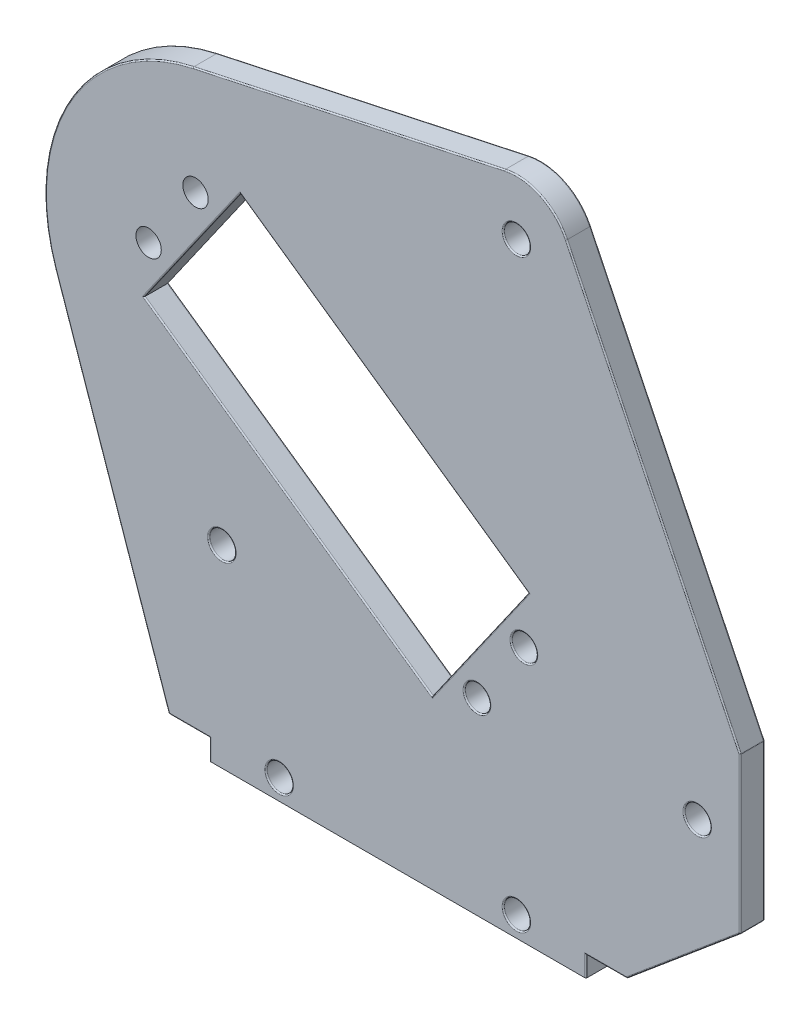
SolidWorks part; units mm, degrees
ref_plane "Front Plane" through (0, 0, 0) normal (0, 0, 1) x (1, 0, 0)
ref_plane "Top Plane" through (0, 0, 0) normal (0, 1, 0) x (1, 0, 0)
ref_plane "Right Plane" through (0, 0, 0) normal (1, 0, 0) x (0, 0, -1)
sketch "Sketch1" plane through (0, 0, 0) normal (0, 0, 1) x (1, 0, 0)
  line L0 (-25.0297, 79.9436) -> (13.0723, 88.1382) construction
  line L1 (41.85, 40.6215) -> (20.6106, 84.4605) construction
  line L2 (41.85, 21.6215) -> (41.85, 40.6215) construction
  line L3 (28, 10) -> (41.85, 21.6215) construction
  line L4 (23, 10) -> (28, 10) construction
  line L5 (23, 0) -> (23, 10) construction
  line L6 (-23, 0) -> (23, 0) construction
  line L7 (-23, 0) -> (-23, 10) construction
  line L8 (-23, 10) -> (-28, 10) construction
  line L9 (-28, 10) -> (-41.8438, 50.1182) construction
  line L10 (-25.0297, 79.9436) -> (13.0723, 88.1382)
  line L11 (41.85, 40.6215) -> (20.6106, 84.4605)
  line L12 (41.85, 21.6215) -> (41.85, 40.6215)
  line L13 (28, 10) -> (41.85, 21.6215)
  line L14 (23, 10) -> (28, 10)
  line L15 (23, 0) -> (23, 10)
  line L16 (-23, 0) -> (23, 0)
  line L17 (-23, 0) -> (-23, 10)
  line L18 (-23, 10) -> (-28, 10)
  line L19 (-28, 10) -> (-41.8438, 50.1182)
  line L20 (0, 0) -> (0, 12.9654) construction
  line L21 (-19.2558, 69.4178) -> (-31.0141, 52.6252)
  line L22 (-19.2558, 69.4178) -> (15.9678, 44.754)
  line L23 (-31.0141, 52.6252) -> (4.2095, 27.9614)
  line L24 (15.9678, 44.754) -> (4.2095, 27.9614)
  line L25 (-25.1349, 61.0215) -> (10.0886, 36.3577) construction
  line L26 (-7.5231, 48.6896) -> (-13.4023, 40.2933) construction
  line L27 (10.0886, 36.3577) -> (16.1909, 32.0848) construction
  arc A0 (20.6106, 84.4605) -> (13.0723, 88.1382) centre (14.5, 81.5) ccw construction
  arc A1 (-25.0297, 79.9436) -> (-41.8438, 50.1182) centre (-20.22, 57.58) ccw construction
  arc A2 (20.6106, 84.4605) -> (13.0723, 88.1382) centre (14.5, 81.5) ccw
  arc A3 (-25.0297, 79.9436) -> (-41.8438, 50.1182) centre (-20.22, 57.58) ccw
  circle A5 centre (9.6782, 30.5412) radius 1.55
  circle A6 centre (15.414, 38.7327) radius 1.55
  circle A7 centre (-24.7245, 66.8379) radius 1.55
  circle A8 centre (-30.4603, 58.6464) radius 1.55
  point P4 (-14.5, 10)
  point P6 (14.5, 10)
  point P8 (36.6, 31.1215)
  point P10 (-21.5, 31.1215)
  point P12 (14.5, 81.5)
  point P17 (41.85, 31.1215)
  point P21 (-20.22, 57.58)
  dimension "D9" = 3
  dimension "D10" = 3.1
  dimension "D1" = 5.25
  dimension "D2" = 10
  dimension "D3" = 21.5
  dimension "D4" = 43
  dimension "D5" = 20.5
  dimension "D6" = 35
  dimension "D7" = 6
  dimension "D8" = 10
extrude "Boss-Extrude1" add sketch "Sketch1" along normal blind 3
hole_wizard "M3 Clearance Hole1" positions "Sketch11" profile "Sketch12" hole size "M3" standard "ISO" end condition through all
sketch "Sketch11" plane through (0, 0, 0) normal (0, 0, -1) x (-1, 0, 0)
  point P0 (-14.5, 81.5)
  point P3 (-36.6, 31.1215)
  point P6 (-14.5, 10)
  point P9 (14.5, 10)
  point P12 (21.5, 31.1215)
sketch "Sketch12" plane through (14.5, 81.5, 0) normal (1, 0, 0) x (0, 1, 0)
  line L0 (0, 0) -> (0, 3)
  line L1 (0, 3) -> (1.6, 3)
  line L2 (1.6, 3) -> (1.6, 0)
  line L5 (1.6, 0) -> (0, 0)
  line L11 (0, -6.35) -> (0, 107.95) construction
  dimension "Thru Hole Dia." = 3.2
  dimension "Thru Hole Depth" = 3
fillet "Fillet1" radius 0.15 52 edges at (12.9, 81.5, 0) (12.9, 81.5, 3) (35, 31.1215, 0) (35, 31.1215, 3) (12.9, 10, 0) (12.9, 10, 3) (-16.1, 10, 0) (-16.1, 10, 3) (-23.1, 31.1215, 0) (-23.1, 31.1215, 3) (8.1282, 30.5412, 0) (8.1282, 30.5412, 3) (16.964, 38.7327, 0) (16.964, 38.7327, 3) (-1.644, 57.0859, 0) (-25.1349, 61.0215, 0) (-13.4023, 40.2933, 0) (10.0886, 36.3577, 0) (-1.644, 57.0859, 3) (-25.1349, 61.0215, 3) (-13.4023, 40.2933, 3) (10.0886, 36.3577, 3) (-40.1467, 68.8136, 0) (-34.9219, 30.0591, 0) (-25.5, 10, 0) (-23, 5, 0) (0, 0, 0) (23, 5, 0) (25.5, 10, 0) (34.925, 15.8108, 0) (41.85, 31.1215, 0) (31.2303, 62.541, 0) (17.4772, 87.6025, 0) (-5.9787, 84.0409, 0) (-40.1467, 68.8136, 3) (-34.9219, 30.0591, 3) (-25.5, 10, 3) (-23, 5, 3) (0, 0, 3) (23, 5, 3) (25.5, 10, 3) (34.925, 15.8108, 3) (41.85, 31.1215, 3) (31.2303, 62.541, 3) (17.4772, 87.6025, 3) (-5.9787, 84.0409, 3) (41.85, 40.6215, 1.5) (41.85, 21.6215, 1.5) (28, 10, 1.5) (-23, 0, 1.5) (-28, 10, 1.5) (23, 0, 1.5)
sketch "Sketch13" plane through (0, 0, 3) normal (0, 0, 1) x (1, 0, 0)
  line L0 (23, 10) -> (23, 0.15) construction
  line L1 (-23, 7.5) -> (23, 7.5)
  line L2 (-23, 7.5) -> (-23, 0)
  line L3 (-23, 0) -> (23, 0)
  line L4 (23, 7.5) -> (23, 0)
  line L5 (22.85, 0) -> (-22.85, 0) construction
  line L6 (-23, 0.15) -> (-23, 10) construction
  dimension "D1" = 7.5
extrude "Cut-Extrude1" cut sketch "Sketch13" against normal through all
